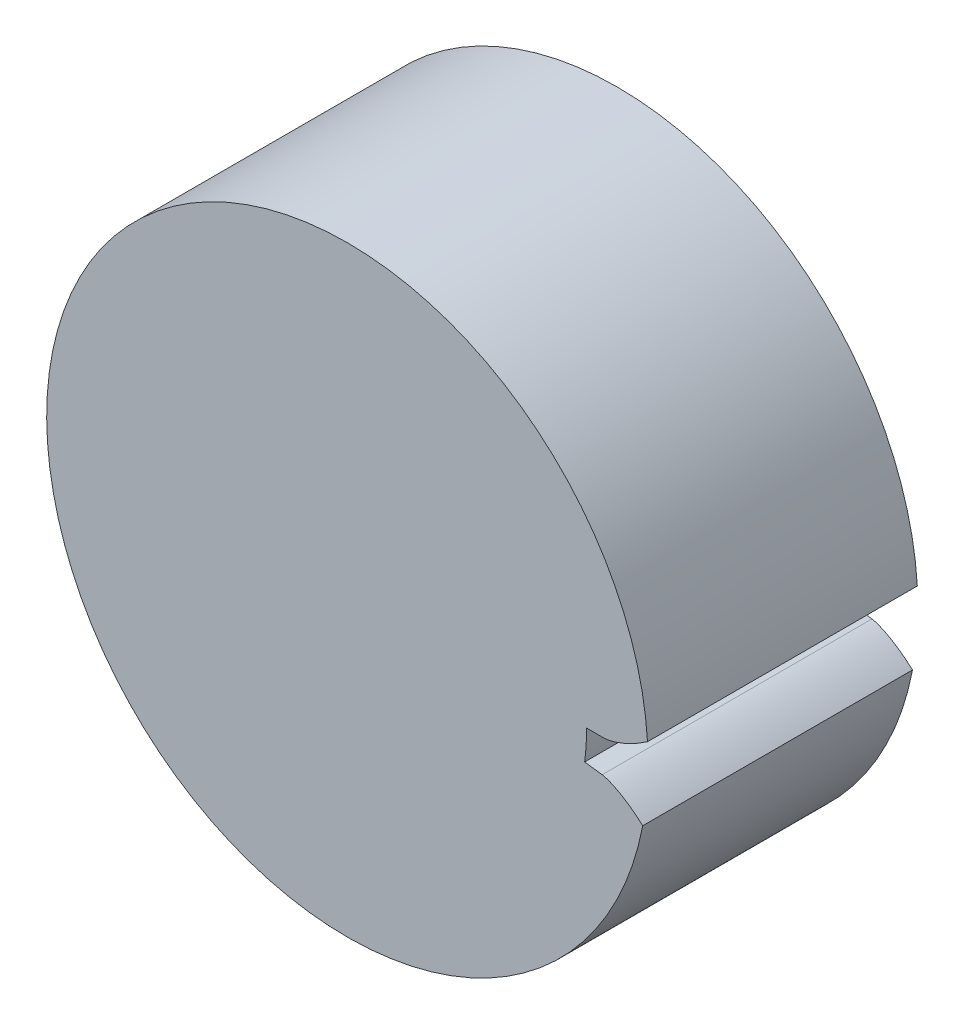
SolidWorks part; units mm, degrees
ref_plane "Front Plane" through (0, 0, 0) normal (0, 0, 1) x (1, 0, 0)
ref_plane "Top Plane" through (0, 0, 0) normal (0, 1, 0) x (1, 0, 0)
ref_plane "Right Plane" through (0, 0, 0) normal (1, 0, 0) x (0, 0, -1)
sketch "Sketch1" plane through (0, 0, 0) normal (0, 0, 1) x (1, 0, 0)
  circle A0 centre (0, 0) radius 24.53
  dimension "D1" = 49.06
extrude "Boss-Extrude1" add sketch "Sketch1" along normal blind 22.0082 contours A0
sketch "Sketch2" plane through (0, 0, 0) normal (0, 0, 1) x (1, 0, 0)
  line L0 (0, 0) -> (20.9551, 0) construction
  line L1 (0, 0) -> (24.4804, -1.5599) construction
  line L2 (0, 0) -> (20.7857, -2.6598) construction
  line L3 (19.5125, 0) -> (20.9551, 0)
  line L4 (19.3547, -2.4767) -> (20.7857, -2.6598)
  circle A0 centre (0, 0) radius 22.3 construction
  circle A1 centre (0, 0) radius 20.9551 construction
  arc A2 (19.3547, -2.4767) -> (19.5125, 0) centre (0, 0) ccw
  circle A3 centre (0, 0) radius 24.53 construction
  spline S0 degree 4 poles (20.9551, 0) (20.9706, 0.0003) (21.0141, 0.0023) (21.096, 0.0099) (21.2291, 0.0281) (21.3976, 0.0595) (21.6139, 0.1097) (21.8662, 0.1807) (22.1405, 0.2715) (22.4351, 0.3835) (22.7254, 0.5071) (23.011, 0.6409) (23.2921, 0.7842) (23.6276, 0.9683) (24.0238, 1.2057) (24.4749, 1.503) (24.9753, 1.8693) (25.4664, 2.2639) (25.9416, 2.6815) (26.397, 3.1144) (26.8392, 3.5705) (27.2581, 4.0326) (27.6711, 4.5261) (28.0007, 4.9429) (28.2995, 5.3493) (28.545, 5.6913) (28.8516, 6.1478) (29.0423, 6.4435) (29.3243, 6.9018) (29.4236, 7.0764) (29.5028, 7.2114) knots 0 0 0 0 0 0.005377 0.015084 0.028532 0.04661 0.064855 0.092111 0.119476 0.146842 0.174209 0.201575 0.228941 0.256307 0.307035 0.361767 0.4165 0.471232 0.525964 0.580697 0.635429 0.690161 0.744894 0.799626 0.826992 0.854358 0.909091 0.954545 1 1 1 1 1 construction
  spline S1 degree 4 poles (20.9551, 0) (20.9706, 0.0003) (21.0141, 0.0023) (21.096, 0.0099) (21.2291, 0.0281) (21.3976, 0.0595) (21.6139, 0.1097) (21.8662, 0.1807) (22.1405, 0.2715) (22.4351, 0.3835) (22.7254, 0.5071) (23.011, 0.6409) (23.2921, 0.7842) (23.6276, 0.9683) (24.0238, 1.2057) (24.4749, 1.503) (24.9753, 1.8693) (25.4664, 2.2639) (25.9416, 2.6815) (26.397, 3.1144) (26.8392, 3.5705) (27.2581, 4.0326) (27.6711, 4.5261) (28.0007, 4.9429) (28.2995, 5.3493) (28.545, 5.6913) (28.7616, 6.0139) (28.8778, 6.1904) (28.9553, 6.311) knots 0 0 0 0 0 0.005377 0.015084 0.028532 0.04661 0.064855 0.092111 0.119476 0.146842 0.174209 0.201575 0.228941 0.256307 0.307035 0.361767 0.4165 0.471232 0.525964 0.580697 0.635429 0.690161 0.744894 0.799626 0.826992 0.854358 0.909091 0.909091 0.909091 0.909091 0.909091
  spline S2 degree 4 poles (20.7857, -2.6598) (20.801, -2.6621) (20.8438, -2.6695) (20.9241, -2.6875) (21.0538, -2.7224) (21.217, -2.775) (21.4251, -2.8522) (21.6664, -2.9547) (21.9269, -3.0795) (22.2049, -3.228) (22.4772, -3.3874) (22.7435, -3.5564) (23.0042, -3.7342) (23.3136, -3.9594) (23.6765, -4.2452) (24.0861, -4.5974) (24.536, -5.0242) (24.9731, -5.4779) (25.3914, -5.9525) (25.7882, -6.4397) (26.169, -6.9482) (26.5258, -7.4598) (26.8728, -8.0017) (27.1468, -8.457) (27.3916, -8.898) (27.5918, -9.2684) (27.8379, -9.7602) (27.9896, -10.0776) (28.2111, -10.568) (28.2875, -10.7538) (28.3488, -10.8978) knots 0 0 0 0 0 0.005377 0.015084 0.028532 0.04661 0.064855 0.092111 0.119476 0.146842 0.174209 0.201575 0.228941 0.256307 0.307035 0.361767 0.4165 0.471232 0.525964 0.580697 0.635429 0.690161 0.744894 0.799626 0.826992 0.854358 0.909091 0.954545 1 1 1 1 1 construction
  spline S3 degree 4 poles (20.7857, -2.6598) (20.801, -2.6621) (20.8438, -2.6695) (20.9241, -2.6875) (21.0538, -2.7224) (21.217, -2.775) (21.4251, -2.8522) (21.6664, -2.9547) (21.9269, -3.0795) (22.2049, -3.228) (22.4772, -3.3874) (22.7435, -3.5564) (23.0042, -3.7342) (23.3136, -3.9594) (23.6765, -4.2452) (24.0861, -4.5974) (24.536, -5.0242) (24.9731, -5.4779) (25.3914, -5.9525) (25.7882, -6.4397) (26.169, -6.9482) (26.5258, -7.4598) (26.8728, -8.0017) (27.1468, -8.457) (27.3916, -8.898) (27.5918, -9.2684) (27.7657, -9.6159) (27.8585, -9.8057) (27.92, -9.9352) knots 0 0 0 0 0 0.005377 0.015084 0.028532 0.04661 0.064855 0.092111 0.119476 0.146842 0.174209 0.201575 0.228941 0.256307 0.307035 0.361767 0.4165 0.471232 0.525964 0.580697 0.635429 0.690161 0.744894 0.799626 0.826992 0.854358 0.909091 0.909091 0.909091 0.909091 0.909091
  dimension "D1" = 44.6
  dimension "D2" = 41.9103
  dimension "D3" = 39.025
  dimension "D4" = 3.646
  dimension "D5" = 3.646
extrude "Cut-Extrude3" cut sketch "Sketch2" against normal through all and the other way through all
equation "\"P`\" = \"N\" / \"dp\"'Diametral pitch - number of teeth per mm"
equation "\"N\" = 20'# of teeth"
equation "\"phi\"= 20deg'Pressure angle"
equation "\"a\"= 1 / \"P`\"'Addendum"
equation "\"b\"= 1.25 / \"P`\"'Dedendum"
equation "\"c\" = \"b\" - \"a\"'clearance"
equation "\"dp\" = 44.60mm'pitch cirle diameter"
equation "\"db\"= \"dp\" * cos ( \"phi\" )'base circle diameter"
equation "\"D1@Sketch1\" = \"dp\" + 2 * \"a\"'Addendum circle diameter"
equation "\"D1@Sketch2\"= \"dp\"'Pitch circle diameter"
equation "\"D2@Sketch2\"= \"db\" 'Base cicrle diameter"
equation "\"alpha\"= sqr ( \"dp\" ^ 2 - \"db\" ^ 2 ) / \"db\" * 180 / pi - \"phi\""
equation "\"dedendum_dia\"= 44.60mm"
equation "\"D3@Sketch2\"= \"dp\" - 2 * \"b\"'Dedendum circle diameter"
equation "\"D4@Sketch2\"= 360 / ( 4 * \"N\" ) - \"alpha\""
equation "\"D5@Sketch2\"= 360 / ( 4 * \"N\" ) - \"alpha\""
